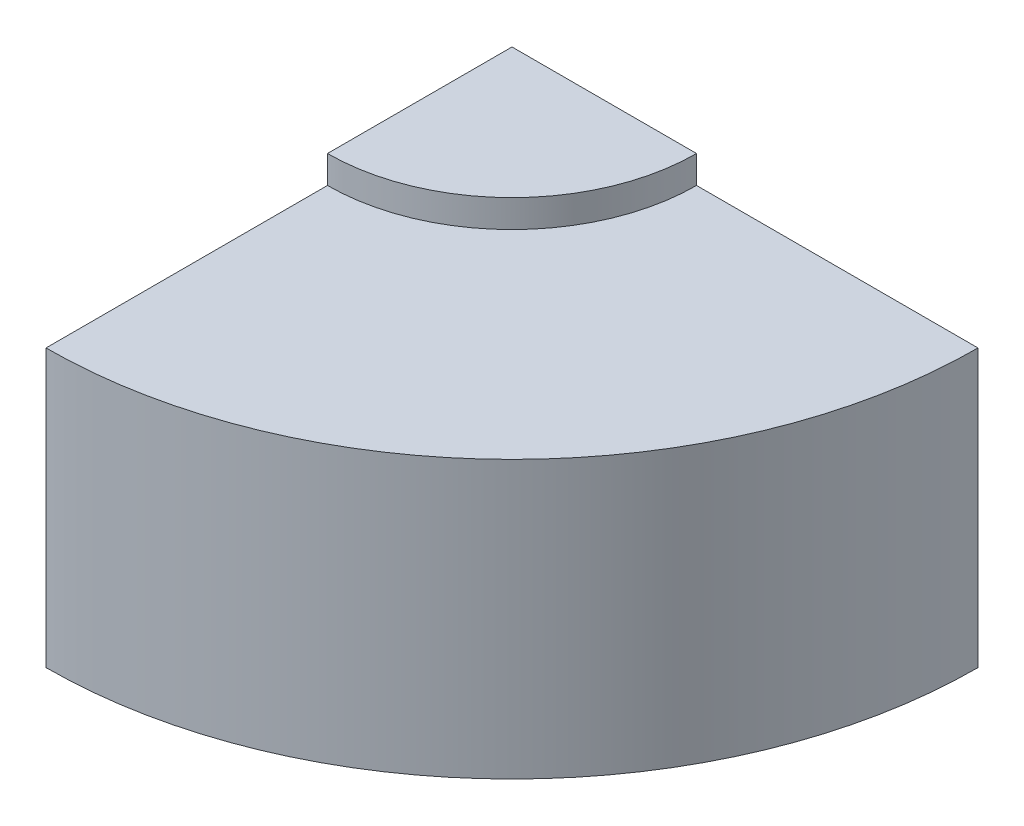
SolidWorks part; units mm, degrees
ref_plane "Front Plane" through (0, 0, 0) normal (0, 0, 1) x (1, 0, 0)
ref_plane "Top Plane" through (0, 0, 0) normal (0, 1, 0) x (1, 0, 0)
ref_plane "Right Plane" through (0, 0, 0) normal (1, 0, 0) x (0, 0, -1)
sketch "Sketch1" plane through (0, 0, 0) normal (0, 0, 1) x (1, 0, 0)
  line L0 (0, 34.1606) -> (0, -41.8394)
  line L1 (0, 34.1606) -> (40, 34.1606)
  line L2 (0, -41.8394) -> (20, -41.8394)
  line L3 (20, -41.8394) -> (20, -31.8394)
  line L4 (20, -31.8394) -> (21, -31.8394)
  line L5 (21, -31.8394) -> (101, -31.8394)
  line L6 (101, -31.8394) -> (101, 28.1606)
  line L7 (40, 34.1606) -> (40, 29.1606)
  line L8 (40, 29.1606) -> (40, 28.1606)
  line L9 (101, 28.1606) -> (21, 28.1606)
  line L10 (21, 28.1606) -> (21, -31.8394)
  line L11 (40, 29.1606) -> (20, 29.1606)
  line L12 (20, 29.1606) -> (20, -31.8394)
  line L13 (101, -21.8394) -> (21, -21.8394)
  line L14 (101, 18.1606) -> (21, 18.1606)
  line L15 (51, 18.1606) -> (51, -21.8394)
  dimension "D1" = 76
  dimension "D2" = 40
  dimension "D3" = 20
  dimension "D4" = 10
  dimension "D5" = 1
  dimension "D6" = 80
  dimension "D7" = 60
  dimension "D8" = 5
  dimension "D9" = 1
  dimension "D10" = 80
  dimension "D11" = 20
  dimension "D12" = 10
  dimension "D13" = 10
  dimension "D14" = 50
revolve "Revolve8" add sketch "Sketch1" angle 90 about L0
